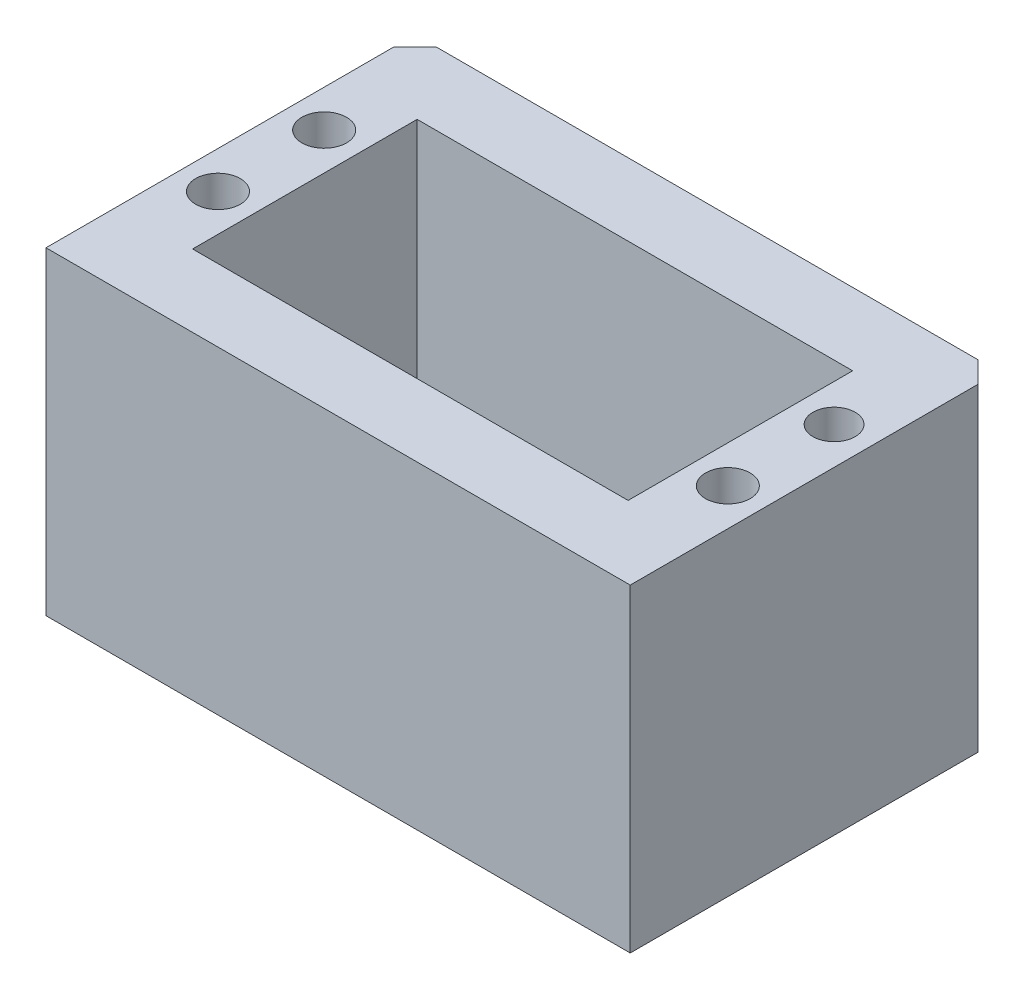
SolidWorks part; units mm, degrees
ref_plane "Front Plane" through (0, 0, 0) normal (0, 0, 1) x (1, 0, 0)
ref_plane "Top Plane" through (0, 0, 0) normal (0, 1, 0) x (1, 0, 0)
ref_plane "Right Plane" through (0, 0, 0) normal (1, 0, 0) x (0, 0, -1)
sketch "Sketch1" plane through (0, 0, 0) normal (0, 1, 0) x (1, 0, 0)
  line L1 (0, 0) -> (55, 0)
  line L2 (0, 0) -> (0, 34.7402)
  line L3 (0, 34.7402) -> (55, 34.7402)
  line L4 (55, 0) -> (55, 34.7402)
  dimension "D1" = 55
  dimension "D2" = 34.7402
extrude "Boss-Extrude1" add sketch "Sketch1" along normal blind 30
sketch "Sketch3" plane through (0, 30, 0) normal (0, 1, 0) x (1, 0, 0)
  line L0 (55, 34.7402) -> (0, 34.7402) construction
  line L1 (7, 27.9402) -> (48, 27.9402)
  line L2 (7, 27.9402) -> (7, 6.8)
  line L3 (7, 6.8) -> (48, 6.8)
  line L4 (48, 27.9402) -> (48, 6.8)
  line L5 (0, 0) -> (55, 0) construction
  line L8 (27.5, 34.7402) -> (27.5, 0) construction
  dimension "D1" = 6.8
  dimension "D2" = 6.8
  dimension "D3" = 41
extrude "Cut-Extrude1" cut sketch "Sketch3" against normal blind 28.87
sketch "Sketch5" plane through (0, 0, 0) normal (-1, 0, 0) x (0, 0, 1)
  line L0 (-34.7402, 30) -> (-34.7402, 0) construction
  line L1 (-21.1902, 8.6) -> (-14.1902, 8.6)
  line L2 (-21.1902, 8.6) -> (-21.1902, 4.4)
  line L3 (-21.1902, 4.4) -> (-14.1902, 4.4)
  line L4 (-14.1902, 8.6) -> (-14.1902, 4.4)
  line L5 (-34.7402, 0) -> (0, 0) construction
  dimension "D1" = 4.2
  dimension "D2" = 13.55
  dimension "7" = 7
  dimension "D3" = 4.4
extrude "Cut-Extrude2" cut sketch "Sketch5" against normal blind 10
sketch "Sketch6" plane through (0, 30, 0) normal (0, 1, 0) x (1, 0, 0)
  circle A0 centre (3.5, 22.6902) radius 2.1
  circle A1 centre (3.5, 12.6902) radius 2.1
  circle A2 centre (51.5, 12.6902) radius 2.1
  circle A3 centre (51.5, 22.6902) radius 1.9931
extrude "Cut-Extrude3" cut sketch "Sketch6" against normal blind 7
sketch "Sketch7" plane through (0, 0, 0) normal (0, -1, 0) x (1, 0, 0)
  circle A0 centre (17.25, -17.6902) radius 4
extrude "Boss-Extrude2" add sketch "Sketch7" along normal blind 12
chamfer "Chamfer1" distance 2 angle 45 2 edges at (55, 15, -34.7402) (0, 15, -34.7402)
